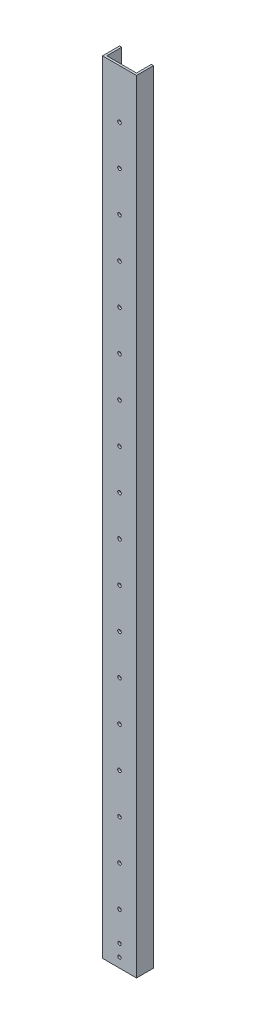
SolidWorks part; units mm, degrees
ref_plane "Front" through (0, 0, 0) normal (0, 0, 1) x (1, 0, 0)
ref_plane "Top" through (0, 0, 0) normal (0, 1, 0) x (1, 0, 0)
ref_plane "Right" through (0, 0, 0) normal (1, 0, 0) x (0, 0, -1)
sketch "Sketch1" plane through (0, 0, 0) normal (0, 1, 0) x (1, 0, 0)
  line L0 (3.175, 3.175) -> (3.175, 25.4)
  line L1 (0, 0) -> (50.8, 0)
  line L2 (0, 0) -> (0, 25.4)
  line L4 (50.8, 0) -> (50.8, 25.4)
  line L5 (3.175, 3.175) -> (47.625, 3.175)
  line L6 (47.625, 3.175) -> (47.625, 25.4)
  line L7 (0, 25.4) -> (3.175, 25.4)
  line L8 (50.8, 25.4) -> (47.625, 25.4)
  dimension "D1" = 25.4
  dimension "D2" = 50.8
  dimension "D3" = 3.175
extrude "Boss-Extrude1" add sketch "Sketch1" along normal blind 1168.4
sketch "Sketch2" plane through (0, 0, 0) normal (0, 0, 1) x (1, 0, 0)
  line L0 (25.4, 0) -> (25.4, 76.2) construction
  line L1 (0, 0) -> (50.8, 0) construction
  circle A0 centre (25.4, 76.2) radius 2.667
  circle A1 centre (25.4, 136.144) radius 2.667
  circle A2 centre (25.4, 196.088) radius 2.667
  circle A3 centre (25.4, 256.032) radius 2.667
  circle A4 centre (25.4, 315.976) radius 2.667
  circle A5 centre (25.4, 375.92) radius 2.667
  circle A6 centre (25.4, 435.864) radius 2.667
  circle A7 centre (25.4, 495.808) radius 2.667
  circle A8 centre (25.4, 555.752) radius 2.667
  circle A9 centre (25.4, 615.696) radius 2.667
  circle A10 centre (25.4, 675.64) radius 2.667
  circle A11 centre (25.4, 735.584) radius 2.667
  circle A12 centre (25.4, 795.528) radius 2.667
  circle A13 centre (25.4, 855.472) radius 2.667
  circle A14 centre (25.4, 915.416) radius 2.667
  circle A15 centre (25.4, 975.36) radius 2.667
  circle A16 centre (25.4, 1035.304) radius 2.667
  circle A17 centre (25.4, 1095.248) radius 2.667
  dimension "D2" = 5.334
  dimension "D1" = 76.2
  dimension "D3" = 18
extrude "Cut-Extrude1" cut sketch "Sketch2" against normal up to next
ref_plane "Mid_Plane" through (25.4, 0, 0) normal (1, 0, 0) x (0, 0, -1)
sketch "Sketch3" plane through (0, 0, 0) normal (0, 0, 1) x (1, 0, 0)
  circle A1 centre (25.4, 32.131) radius 2.5527
  circle A3 centre (25.4, 14.2875) radius 2.5527
extrude "Cut-Extrude2" cut sketch "Sketch3" against normal up to next
sketch "Sketch4" plane through (0, 0, 0) normal (-1, 0, 0) x (0, 0, 1)
  line L0 (-19.05, 76.2) -> (-19.05, 0) construction
  line L1 (-25.4, 0) -> (0, 0) construction
  line L2 (-19.05, 76.2) -> (-25.4, 76.2) construction
  line L3 (-25.4, 1168.4) -> (-25.4, 0) construction
  line L4 (-19.05, 76.2) -> (-19.05, 136.144) construction
  circle A0 centre (-19.05, 76.2) radius 2.667
  circle A1 centre (-19.05, 136.144) radius 2.667
  circle A2 centre (-19.05, 196.088) radius 2.667
  circle A3 centre (-19.05, 256.032) radius 2.667
  circle A4 centre (-19.05, 315.976) radius 2.667
  circle A5 centre (-19.05, 375.92) radius 2.667
  circle A6 centre (-19.05, 435.864) radius 2.667
  circle A7 centre (-19.05, 495.808) radius 2.667
  circle A8 centre (-19.05, 555.752) radius 2.667
  circle A9 centre (-19.05, 615.696) radius 2.667
  circle A10 centre (-19.05, 675.64) radius 2.667
  circle A11 centre (-19.05, 735.584) radius 2.667
  circle A12 centre (-19.05, 795.528) radius 2.667
  circle A13 centre (-19.05, 855.472) radius 2.667
  circle A14 centre (-19.05, 915.416) radius 2.667
  circle A15 centre (-19.05, 975.36) radius 2.667
  circle A16 centre (-19.05, 1035.304) radius 2.667
  circle A17 centre (-19.05, 1095.248) radius 2.667
  dimension "D1" = 5.334
  dimension "D2" = 6.35
  dimension "D3" = 76.2
  dimension "D5" = 59.944
  dimension "D4" = 18
extrude "Cut-Extrude3" cut sketch "Sketch4" against normal up to next
